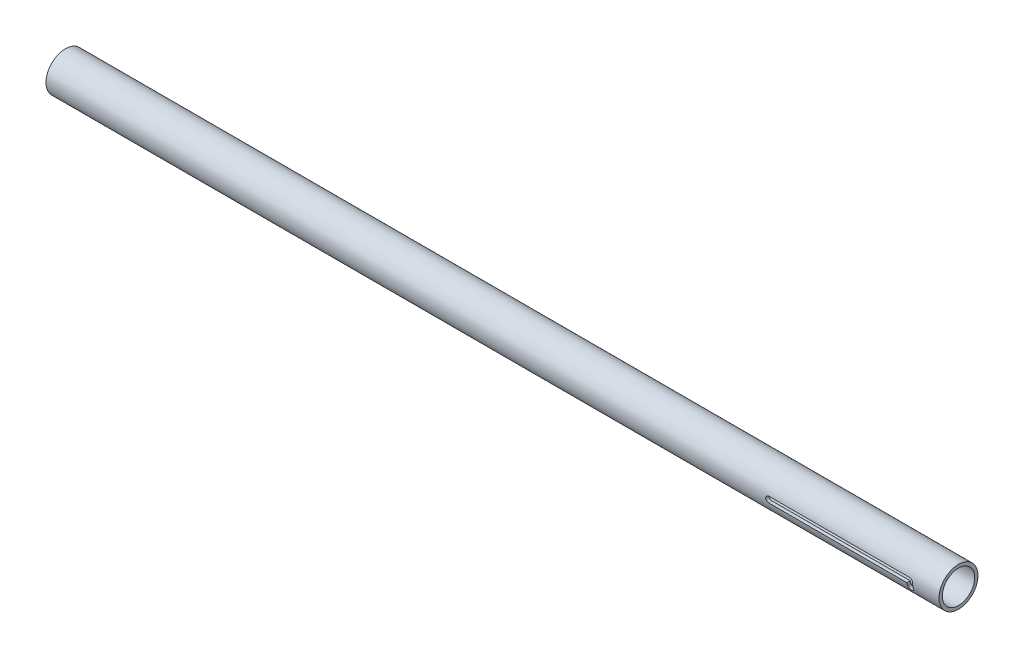
SolidWorks part; units mm, degrees
material "6061-T6 (SS)"
ref_plane "Front Plane" through (0, 0, 0) normal (0, 0, 1) x (1, 0, 0)
ref_plane "Top Plane" through (0, 0, 0) normal (0, 1, 0) x (1, 0, 0)
ref_plane "Right Plane" through (0, 0, 0) normal (1, 0, 0) x (0, 0, -1)
sketch "Sketch1" plane through (0, 0, 0) normal (1, 0, 0) x (0, 0, -1)
  circle A0 centre (0, 0) radius 21.082
  circle A1 centre (0, 0) radius 17.526
  dimension "D1" = 42.164
  dimension "D2" = 35.052
extrude "Boss-Extrude1" add sketch "Sketch1" along normal blind 965.2
sketch "Sketch2" plane through (0, 0, 0) normal (0, 0, 1) x (1, 0, 0)
  line L0 (7.9375, 0) -> (20.6375, 0) construction
  line L1 (7.9375, 3.175) -> (20.6375, 3.175)
  line L2 (7.9375, -3.175) -> (20.6375, -3.175)
  line L3 (46.0375, 0) -> (58.7375, 0) construction
  line L4 (46.0375, 3.175) -> (58.7375, 3.175)
  line L5 (46.0375, -3.175) -> (58.7375, -3.175)
  line L6 (0, 21.082) -> (0, -21.082) construction
  arc A0 (7.9375, 3.175) -> (7.9375, -3.175) centre (7.9375, 0) ccw
  arc A1 (20.6375, -3.175) -> (20.6375, 3.175) centre (20.6375, 0) ccw
  arc A2 (46.0375, 3.175) -> (46.0375, -3.175) centre (46.0375, 0) ccw
  arc A3 (58.7375, -3.175) -> (58.7375, 3.175) centre (58.7375, 0) ccw
  point P3 (14.2875, 0)
  point P8 (52.3875, 0)
  dimension "D1" = 7.9375
  dimension "D2" = 38.1
  dimension "D3" = 12.7
  dimension "D4" = 6.35
extrude "Cut-Extrude1" cut sketch "Sketch2" against normal through all
sketch "Sketch3" plane through (0, 0, 0) normal (0, 0, 1) x (1, 0, 0)
  line L0 (965.2, -21.082) -> (965.2, 21.082) construction
  line L1 (781.05, 3.175) -> (933.45, 3.175)
  line L2 (781.05, -3.175) -> (930.275, -3.175)
  line L3 (930.275, -6.35) -> (930.275, -3.175)
  line L4 (936.625, 0) -> (936.625, -6.35)
  arc A0 (936.625, 0) -> (933.45, 3.175) centre (933.45, 0) ccw
  arc A1 (781.05, 3.175) -> (781.05, -3.175) centre (781.05, 0) ccw
  arc A3 (930.275, -6.35) -> (936.625, -6.35) centre (933.45, -6.35) ccw
  dimension "D1" = 6.35
  dimension "D2" = 31.75
  dimension "D3" = 152.4
  dimension "D4" = 6.35
extrude "Cut-Extrude2" cut sketch "Sketch3" along normal through all
